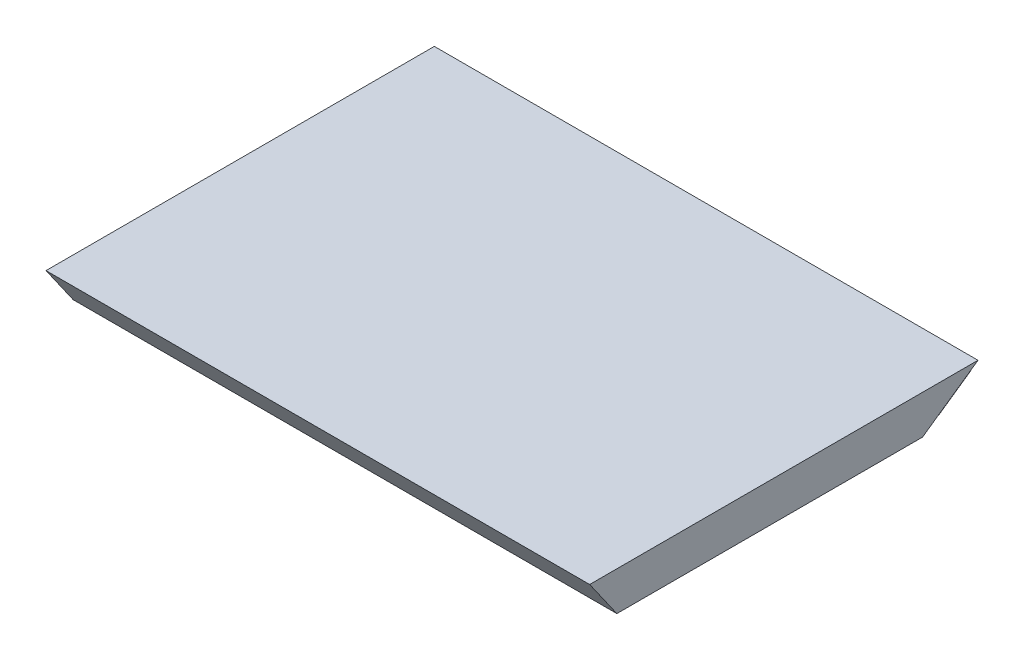
SolidWorks part; units mm, degrees
material "Maple"
ref_plane "Front Plane" through (0, 0, 0) normal (0, 0, 1) x (1, 0, 0)
ref_plane "Top Plane" through (0, 0, 0) normal (0, 1, 0) x (1, 0, 0)
ref_plane "Right Plane" through (0, 0, 0) normal (1, 0, 0) x (0, 0, -1)
sketch "Sketch2" plane through (0, 0, 0) normal (1, 0, 0) x (0, 0, -1)
  line L0 (31.75, 3.175) -> (22.6813, -3.175)
  line L1 (-31.75, 3.175) -> (31.75, 3.175)
  line L2 (-31.75, 3.175) -> (-31.75, -3.175)
  line L3 (-31.75, -3.175) -> (31.75, -3.175)
  line L4 (31.75, 3.175) -> (31.75, -3.175)
  line L5 (-31.75, 3.175) -> (31.75, -3.175) construction
  line L6 (-31.75, -3.175) -> (31.75, 3.175) construction
  line L7 (-31.75, 3.175) -> (-27.3037, -3.175)
  point P0 (0, 0)
  dimension "D1" = 63.5
  dimension "D2" = 6.35
  dimension "D3" = 35
  dimension "D4" = 35
extrude "Boss-Extrude2" add sketch "Sketch2" along normal mid plane 88.9 contours L2 L3 L0 L1
sketch "Sketch3" plane through (0, 3.175, 0) normal (0, 1, 0) x (1, 0, 0)
  line L0 (44.45, 31.75) -> (-44.45, 31.75) construction
  line L1 (44.45, -31.75) -> (-44.45, -31.75) construction
  line L2 (44.45, 31.75) -> (-44.45, 31.75)
  line L3 (44.45, -31.75) -> (-44.45, -31.75)
  line L4 (-25.3777, 31.75) -> (25.3777, 31.75)
  arc A0 (-25.3777, 31.75) -> (25.3777, 31.75) centre (0, 31.75) ccw
extrude "Cut-Extrude1" [suppressed] cut sketch "Sketch3" against normal through all contours L2 A0
sketch "Sketch4" plane through (0, -12.7872, -8.9537) normal (0, -0.8192, -0.5736) x (1, 0, 0)
  line L0 (44.45, -27.8292) -> (-44.45, -27.8292) construction
  line L1 (-38.1, -21.4792) -> (38.1, -21.4792)
  line L2 (-38.1, -21.4792) -> (-38.1, -27.8292)
  line L3 (-38.1, -27.8292) -> (38.1, -27.8292)
  line L4 (38.1, -21.4792) -> (38.1, -27.8292)
  line L6 (-44.45, -27.8292) -> (-44.45, -16.7583) construction
  line L7 (44.45, -27.8292) -> (44.45, -16.7583) construction
  point P6 (-44.45, -22.2937)
  point P13 (44.45, -22.2937)
  dimension "D1" = 6.35
  dimension "D2" = 6.35
  dimension "D3" = 6.35
extrude "Boss-Extrude3" add sketch "Sketch4" along normal blind 8.89
